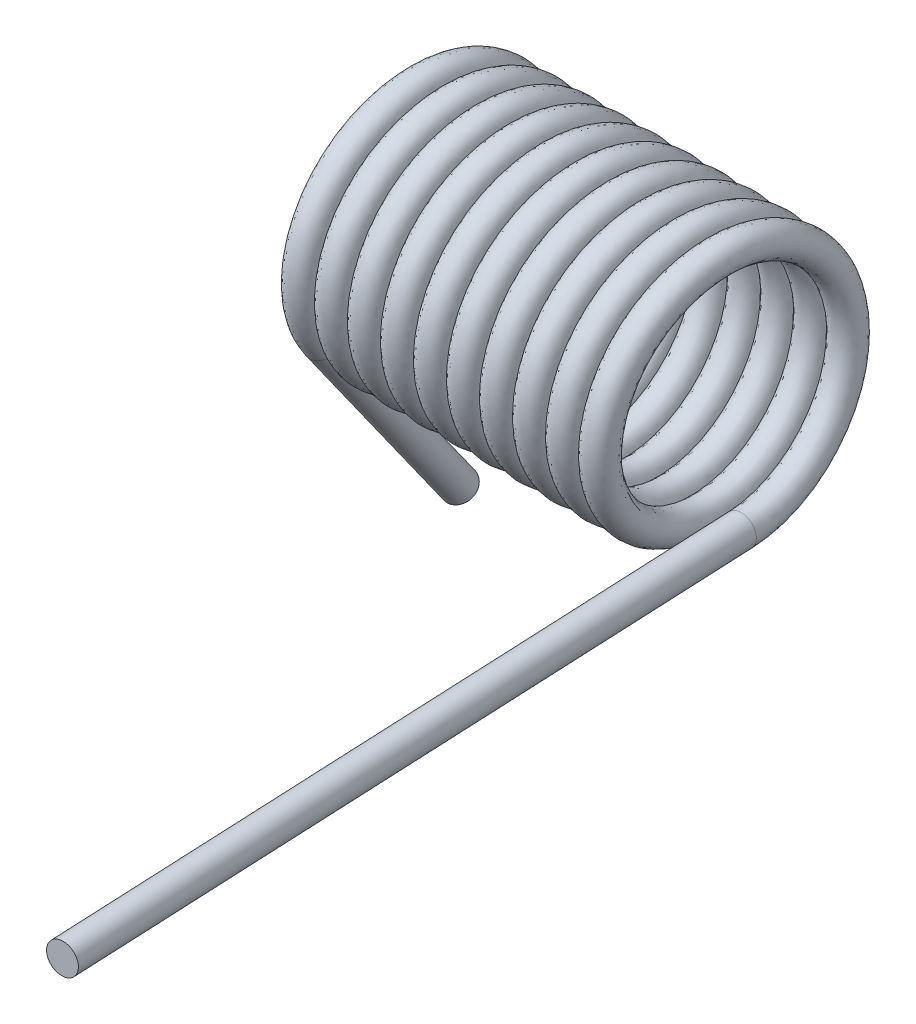
SolidWorks part; units mm, degrees
ref_plane "Front" through (0, 0, 0) normal (0, 0, 1) x (1, 0, 0)
ref_plane "Top" through (0, 0, 0) normal (0, 1, 0) x (1, 0, 0)
ref_plane "Right" through (0, 0, 0) normal (1, 0, 0) x (0, 0, -1)
sketch "Sketch1" plane through (0, 0, 0) normal (1, 0, 0) x (0, 0, -1)
  line L0 (0, -1.0033) -> (0, -1.3081) construction
  line L1 (-1.3081, 0) -> (-1.3081, -9.525) construction
  line L2 (0, -1.3081) -> (-9.525, -1.3081) construction
  line L3 (0, 0) -> (1.3081, 0) construction
  line L4 (0, 0) -> (-1.3081, 0) construction
  line L5 (-9.525, -1.3081) -> (-9.525, -1.0033) construction
  line L6 (-9.525, -1.0033) -> (0, -1.0033) construction
  line L7 (-1.3081, -9.525) -> (-1.0033, -9.525) construction
  line L8 (-1.0033, -9.525) -> (-1.0033, 0) construction
  circle A0 centre (0, 0) radius 1.3081 construction
  circle A1 centre (0, 0) radius 0.762 construction
  circle A2 centre (0, 0) radius 1.1557 construction
  point P7 (0, -1.1557)
  point P10 (0, 1.3081)
  dimension "OD" = 2.6162
  dimension "For Shaft Diameter" = 1.524
  dimension "Wire Diameter" = 0.3048
  dimension "Leg Length" = 9.525
  dimension "Deflection Angle" = 270
sketch "Sketch2" plane through (0, 0, 0) normal (1, 0, 0) x (0, 0, -1)
  circle A0 centre (0, 0) radius 1.1557 construction
  circle A2 centre (0, 0) radius 1.1557
curve "Helix/Spiral1" pitch 0.3302 height 3.2525 turns 9.85
ref_plane "Plane1" through (0, -1.1557, 0) normal (-0.0454, 0, -0.999) x (0.9987, -0.0232, -0.0454)
sketch "Sketch3" plane through (0, -1.1557, 0) normal (-0.0454, 0, -0.999) x (0.9987, -0.0232, -0.0454)
  circle A0 centre (0, 0) radius 0.1524
  dimension "D1" = 0.3048
sweep "Sweep1" add profiles "Sketch3" path "Helix/Spiral1"
sketch "Sketch4" plane through (0, 0, 0) normal (0.0454, 0, 0.999) x (-0.9987, 0.0232, 0.0454)
  circle A1 centre (-0.0269, 1.1554) radius 0.1524
  circle A2 centre (-0.0269, 1.1554) radius 0.1524
  dimension "D1" = 0
extrude "Extrude1" add sketch "Sketch4" along normal blind 7.112
sketch "Sketch5" plane through (-0.0067, -0.1194, -0.0868) normal (-0.0454, -0.8082, -0.5872) x (0.9528, 0.1416, -0.2687)
  circle A1 centre (-3.4462, 0.1255) radius 0.1524
  circle A2 centre (-3.4462, 0.1255) radius 0.1524
  dimension "D1" = 0
extrude "Extrude2" add sketch "Sketch5" along normal blind 2.54
sketch "Sketch6" plane through (0, 0, 0) normal (1, 0, 0) x (0, 0, -1)
  line L0 (0, 0) -> (-0.5207, 0.8576) construction
  circle A0 centre (0, 0) radius 1.0033
  circle A2 centre (0, 0) radius 1.0033 construction
sketch "Sketch7" plane through (0, 0, 0) normal (0, 1, 0) x (1, 0, 0)
  line L0 (0, 0) -> (-4.8058, 0) construction
equation "\"D4@Helix/Spiral1\" = \"Wire Diameter@Sketch1\" + .001"
equation "\"D1@Sketch3\"=\"Wire Diameter@Sketch1\""
